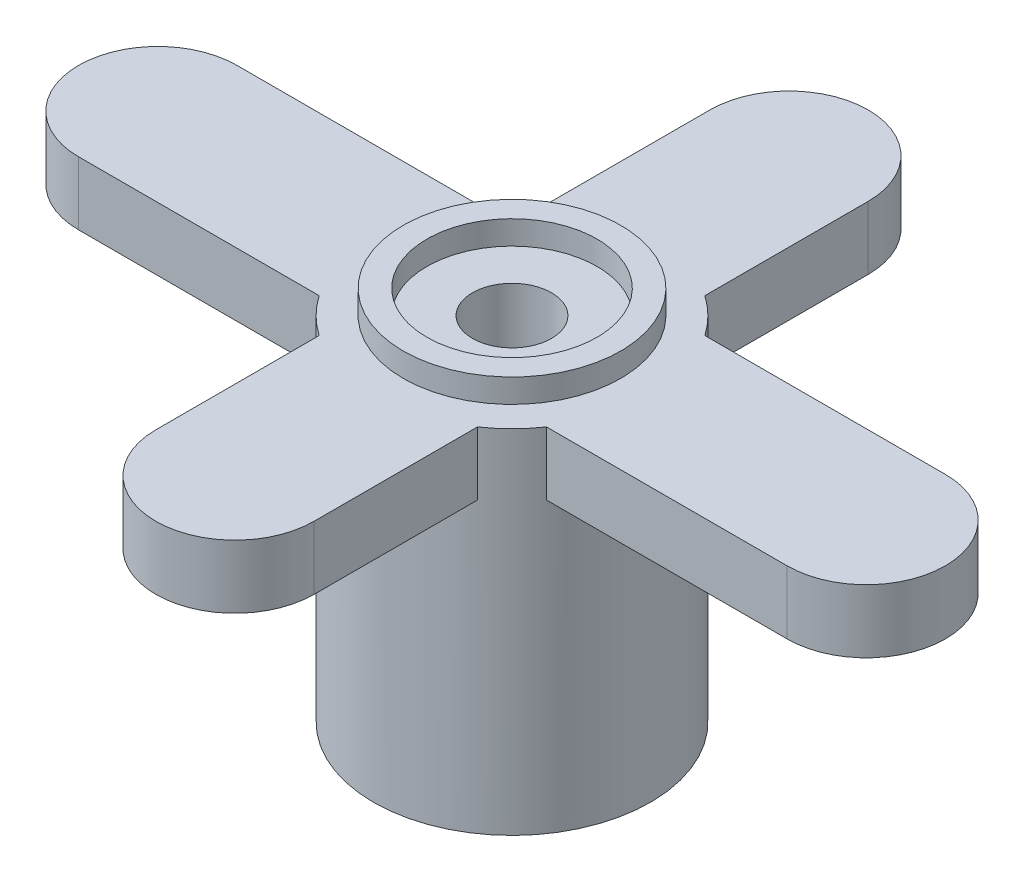
SolidWorks part; units mm, degrees
ref_plane "Płaszczyzna przednia" through (0, 0, 0) normal (0, 0, 1) x (1, 0, 0)
ref_plane "Płaszczyzna górna" through (0, 0, 0) normal (0, 1, 0) x (1, 0, 0)
ref_plane "Płaszczyzna prawa" through (0, 0, 0) normal (1, 0, 0) x (0, 0, -1)
sketch "Szkic1" plane through (0, 0, 0) normal (0, 1, 0) x (1, 0, 0)
  circle A0 centre (0, 0) radius 3.5
  dimension "D1" = 7
extrude "Dodanie-wyciągnięcie1" add sketch "Szkic1" along normal blind 9.5
sketch "Szkic2" plane through (0, 0, 0) normal (0, -1, 0) x (1, 0, 0)
  circle A0 centre (0, 0) radius 1.9
  dimension "D1" = 3.8
extrude "Wytnij-wyciągnięcie1" cut sketch "Szkic2" against normal blind 3.5
ref_plane "Płaszczyzna1" through (0, 8.9, 0) normal (0, 1, 0) x (1, 0, 0)
sketch "Szkic3" plane through (0, 8.9, 0) normal (0, 1, 0) x (1, 0, 0)
  line L0 (0, 0) -> (15.3312, 0) construction
  line L1 (0, 0) -> (0, 11.7192) construction
  line L2 (-8.95, 2) -> (0, 2)
  line L3 (0, 2) -> (8.95, 2)
  line L4 (-8.95, -2) -> (8.95, -2)
  line L5 (-2, -7) -> (-2, 7)
  line L6 (2, -7) -> (2, 0)
  line L7 (2, 0) -> (2, 7)
  circle A0 centre (8.95, 0) radius 2
  circle A1 centre (-8.95, 0) radius 2
  circle A2 centre (0, 7) radius 2
  circle A3 centre (0, -7) radius 2
  dimension "D1" = 4
  dimension "D2" = 4
  dimension "D4" = 4
  dimension "D5" = 4
  dimension "D3" = 17.9
  dimension "D6" = 14
extrude "Dodanie-wyciągnięcie2" add sketch "Szkic3" against normal blind 1.6 contours A1 | A1 L4 L5 L2 | A2 | A2 L5 L2 L3 L7 | A0 L3 L7 L6 L4 | A0 | A3 | A3 L6 L4 L5
sketch "Szkic4" plane through (0, 9.5, 0) normal (0, 1, 0) x (1, 0, 0)
  circle A0 centre (0, 0) radius 2.15
  dimension "D1" = 4.3
extrude "Wytnij-wyciągnięcie2" cut sketch "Szkic4" against normal up to surface (0.6 mm away)
sketch "Szkic5" plane through (0, 8.9, 0) normal (0, 1, 0) x (1, 0, 0)
  circle A0 centre (0, 0) radius 1
  dimension "D1" = 2
extrude "Wytnij-wyciągnięcie3" cut sketch "Szkic5" against normal blind 31.6
sketch "Szkic6" plane through (0, 9.5, 0) normal (0, 1, 0) x (1, 0, 0)
  circle A0 centre (0, 0) radius 3.5 construction
  circle A1 centre (0, 0) radius 2.75
  circle A2 centre (0, 0) radius 3.5
  dimension "D1" = 5.5
extrude "Wytnij-wyciągnięcie4" cut sketch "Szkic6" against normal up to surface (0.6 mm away) up to face at (-6.5681, 8.9, 0)
